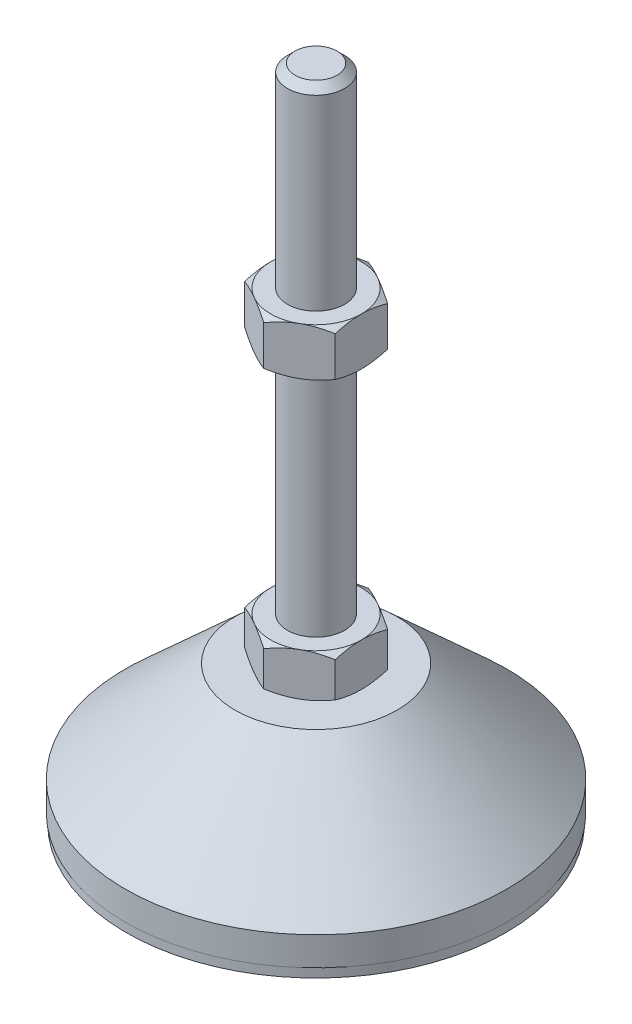
SolidWorks part; units mm, degrees
ref_plane "Спереди" through (0, 0, 0) normal (0, 0, 1) x (1, 0, 0)
ref_plane "Сверху" through (0, 0, 0) normal (0, 1, 0) x (1, 0, 0)
ref_plane "Справа" through (0, 0, 0) normal (1, 0, 0) x (0, 0, -1)
sketch "Эскиз1" plane through (0, 0, 0) normal (0, 0, 1) x (1, 0, 0)
  line L0 (0, 0) -> (-39.8, 0)
  line L1 (-39.8, 0) -> (-39.8, 2)
  line L2 (-39.8, 2) -> (-40, 2)
  line L3 (-40, 2) -> (-40, 8)
  line L4 (-40, 8) -> (-17, 29)
  line L5 (-17, 29) -> (-6, 29)
  line L12 (-6, 38) -> (-6, 136.4)
  line L13 (-6, 136.4) -> (-4.4, 138)
  line L14 (-4.4, 138) -> (0, 138)
  line L15 (0, 138) -> (0, 0) construction
  line L16 (-6, 29) -> (0, 29) construction
  line L17 (0, 0) -> (0, 138)
  line L18 (0, 0) -> (0, -7.9595) construction
  line L19 (-6, 38) -> (-6, 29)
  point P8 (-6, 87.2)
  point P23 (-11.5, 29)
  dimension "D1" = 12
  dimension "D2" = 29
  dimension "D3" = 9
  dimension "D4" = 80
  dimension "D5" = 6
  dimension "D6" = 1.6
  dimension "D7" = 45
  dimension "D8" = 34
  dimension "D9" = 2
  dimension "D10" = 100
  dimension "D11" = 6
  dimension "D12" = 0.2
revolve "Повернуть1" add sketch "Эскиз1" angle 360 about L17
sketch "Эскиз2" plane through (0, 29, 0) normal (0, 1, 0) x (1, 0, 0)
  line L1 (0, 10.9697) -> (-9.5, 5.4848)
  line L2 (-9.5, 5.4848) -> (-9.5, -5.4848)
  line L3 (-9.5, -5.4848) -> (0, -10.9697)
  line L4 (0, -10.9697) -> (9.5, -5.4848)
  line L5 (9.5, -5.4848) -> (9.5, 5.4848)
  line L6 (9.5, 5.4848) -> (0, 10.9697)
  circle A0 centre (0, 0) radius 9.5 construction
  dimension "D1" = 19
extrude "Бобышка-Вытянуть1" add sketch "Эскиз2" along normal up to vertex (9 mm away) up to point (-6, 38, 0)
ref_plane "Плоскость1" through (0, 87.2, 0) normal (0, 1, 0) x (1, 0, 0)
sketch "Эскиз3" plane through (0, 87.2, 0) normal (0, 1, 0) x (1, 0, 0)
  line L6 (9.5, 5.4848) -> (0, 10.9697)
  line L7 (0, 10.9697) -> (-9.5, 5.4848)
  line L8 (-9.5, 5.4848) -> (-9.5, -5.4848)
  line L9 (-9.5, -5.4848) -> (0, -10.9697)
  line L10 (0, -10.9697) -> (9.5, -5.4848)
  line L11 (9.5, -5.4848) -> (9.5, 5.4848)
  line L12 (9.5, 5.4848) -> (0, 10.9697)
  line L13 (0, 10.9697) -> (-9.5, 5.4848)
  line L14 (-9.5, 5.4848) -> (-9.5, -5.4848)
  line L15 (-9.5, -5.4848) -> (0, -10.9697)
  line L16 (0, -10.9697) -> (9.5, -5.4848)
  line L17 (9.5, -5.4848) -> (9.5, 5.4848)
  dimension "D1" = 0
extrude "Бобышка-Вытянуть2" add sketch "Эскиз3" along normal blind 10
sketch "Эскиз4" plane through (0, 0, 0) normal (0, 0, 1) x (1, 0, 0)
  line L0 (-9.5, 97.2) -> (-18.1603, 92.2)
  line L1 (-18.1603, 92.2) -> (-18.1603, 97.2)
  line L2 (-18.1603, 97.2) -> (-9.5, 97.2)
  line L3 (-18.1603, 92.2) -> (-9.5, 87.2)
  line L4 (50, 87.2) -> (-50, 87.2) construction
  line L5 (-9.5, 87.2) -> (-18.1603, 87.2)
  line L6 (-18.1603, 87.2) -> (-18.1603, 92.2)
  line L7 (-9.5, 97.2) -> (-9.5, 87.2) construction
  line L8 (-9.5, 38) -> (-17.2942, 38)
  line L9 (-17.2942, 38) -> (-17.2942, 33.5)
  line L10 (-17.2942, 33.5) -> (-9.5, 38)
  line L11 (-9.5, 29) -> (-17.2942, 33.5)
  line L12 (-17.2942, 33.5) -> (-17.2942, 29)
  line L13 (-17.2942, 29) -> (-9.5, 29)
  line L14 (0, 138) -> (0, 96.3793) construction
  dimension "D1" = 30
  dimension "D2" = 30
revolve "Вырез-Повернуть2" cut sketch "Эскиз4" angle 360 about L14
